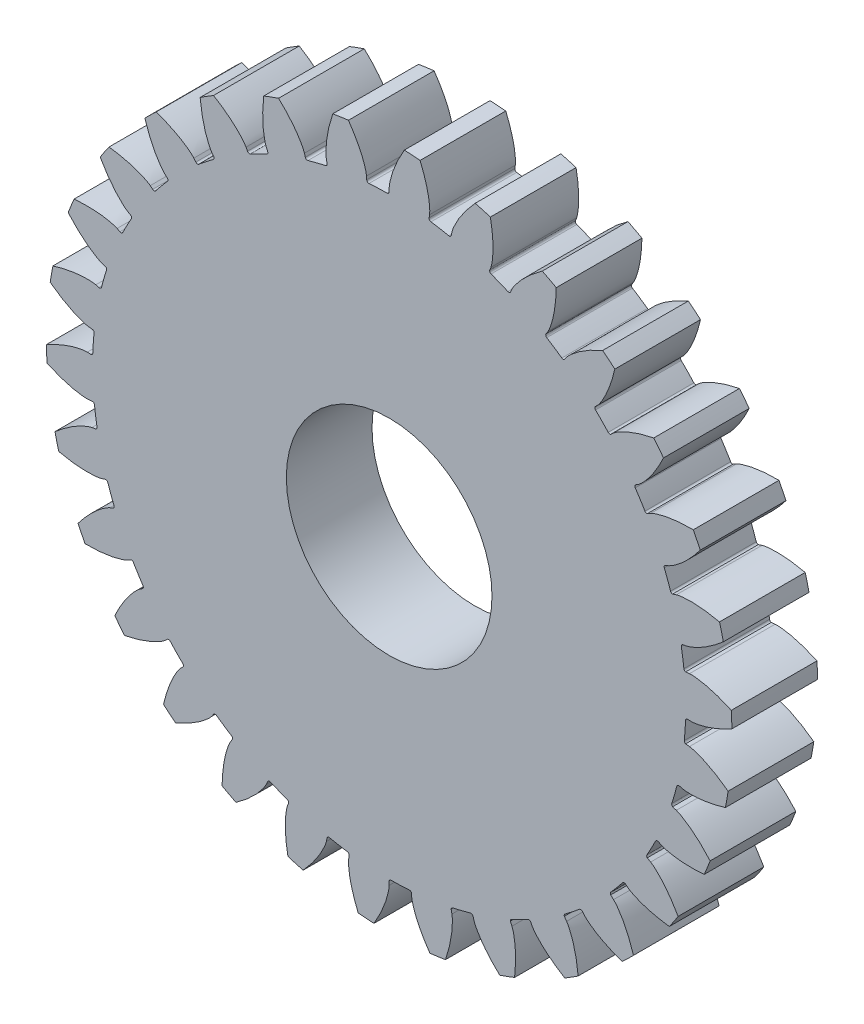
SolidWorks part; units mm, degrees
ref_plane "Alzado" through (0, 0, 0) normal (0, 0, 1) x (1, 0, 0)
ref_plane "Planta" through (0, 0, 0) normal (0, 1, 0) x (1, 0, 0)
ref_plane "Vista lateral" through (0, 0, 0) normal (1, 0, 0) x (0, 0, -1)
sketch "Croquis1" plane through (0, 0, 0) normal (0, 0, 1) x (1, 0, 0)
  line L0 (0, 0) -> (131.0885, 0) construction
  line L1 (0, 0) -> (0, 30) construction
  line L2 (0, 0) -> (12.4587, 12.4587) construction
  line L3 (12.4587, 12.4587) -> (2.6737, 22.2437) construction
  line L4 (0, 0) -> (11.3254, 13.4971) construction
  line L5 (11.3254, 13.4971) -> (1.9027, 21.4038) construction
  line L6 (0, 0) -> (10.106, 14.4328) construction
  line L7 (10.106, 14.4328) -> (1.2895, 20.6062) construction
  line L8 (0, 0) -> (8.8096, 15.2587) construction
  line L9 (8.8096, 15.2587) -> (0.8202, 19.8714) construction
  line L10 (0, 0) -> (7.4462, 15.9685) construction
  line L11 (7.4462, 15.9685) -> (0.4787, 19.2175) construction
  line L12 (0, 0) -> (6.0261, 16.5567) construction
  line L13 (6.0261, 16.5567) -> (0.2468, 18.6602) construction
  line L14 (0, 0) -> (4.5602, 17.0189) construction
  line L15 (4.5602, 17.0189) -> (0.1047, 18.2127) construction
  line L16 (0, 0) -> (3.0595, 17.3516) construction
  line L17 (3.0595, 17.3516) -> (0.0311, 17.8856) construction
  line L18 (0, 0) -> (1.5356, 17.5522) construction
  line L19 (1.5356, 17.5522) -> (0.0039, 17.6862) construction
  circle A0 centre (0, 0) radius 17.6192 construction
  circle A1 centre (0, 0) radius 17.3038 construction
  circle A2 centre (0, 0) radius 20 construction
  circle A3 centre (0, 0) radius 18.75 construction
  spline S0 degree 3 poles (0, 17.6192) (0.003, 17.7087) (0.0309, 17.9084) (0.1107, 18.2574) (0.255, 18.7048) (0.4889, 19.2621) (0.8326, 19.916) (1.5096, 20.9709) (2.1682, 21.7377) (2.6737, 22.2437) knots 0 0 0 0 0.049384 0.111113 0.197533 0.308643 0.444446 0.604939 1 1 1 1
  point P3 (87.284, 1.25)
  point P4 (102.0506, 30)
  point P5 (119.8936, 20)
  point P29 (0, 17.6192)
  dimension "Diámetro de paso (D)" = 37.5
  dimension "Diámetro de raiz" = 34.6075
  dimension "D1" = 40
  dimension "D2" = 35.2385
  dimension "Módulo (m)" = 1.25
  dimension "Número de dientes (N)" = 30
  dimension "Ángulo de presión (AP)" = 20
  dimension "D3" = 45
  dimension "D4" = 13.8381
  dimension "D5" = 40
  dimension "D6" = 12.3005
  dimension "D7" = 35
  dimension "D8" = 10.763
  dimension "D9" = 9.2254
  dimension "D10" = 30
  dimension "D11" = 25
  dimension "D12" = 7.6878
  dimension "D13" = 20
  dimension "D14" = 6.1503
  dimension "D15" = 15
  dimension "D16" = 4.6127
  dimension "D17" = 10
  dimension "D18" = 3.0751
  dimension "D19" = 5
  dimension "D20" = 1.5376
sketch "Croquis2" plane through (0, 0, 0) normal (0, 0, 1) x (1, 0, 0)
  line L0 (56.3227, 9.5882) -> (76.5884, 9.5882) construction
  line L1 (0, 17.3911) -> (0, 17.6192)
  line L2 (0, 0) -> (0.3802, 25.5087) construction
  line L3 (0, 0) -> (3.1082, 25.8589) construction
  line L4 (0, 0) -> (32.6464, 0) construction
  line L5 (0, 0) -> (131.0885, 0) construction
  line L6 (0, 0) -> (1.6991, 25.221) construction
  line L7 (2.3325, 17.2754) -> (2.3632, 17.46)
  line L8 (57.5292, -20.4598) -> (78.7754, -20.4598) construction
  circle A0 centre (0, 0) radius 17.3038 construction
  circle A1 centre (0, 0) radius 20 construction
  arc A2 (-0.1185, 17.3033) -> (2.4382, 17.1311) centre (0, 0) ccw
  arc A3 (1.8037, 19.9185) -> (0.8841, 19.9804) centre (0, 0) ccw
  circle A4 centre (0, 0) radius 18.75 construction
  circle A5 centre (0, 0) radius 6
  arc A6 (2.3325, 17.2754) -> (2.4382, 17.1311) centre (2.4558, 17.2549) ccw
  arc A7 (0, 17.3911) -> (-0.1185, 17.3033) centre (-0.1193, 17.4283) cw
  spline S0 degree 3 poles (1999.6387, -5.2987) (13.6797, 2.6109) (-1.3181, 12.0138) (0.1107, 18.2574) (0.255, 18.7048) (0.4889, 19.2621) (0.8326, 19.916) (20.139, 49.9979) (181.5845, -20.662) (-1997.0603, 11.1311) knots -3.336491 -3.336491 -3.336491 -3.336491 0.049384 0.111113 0.197533 0.308643 0.444446 0.604939 20.022687 20.022687 20.022687 20.022687 only from (0, 17.6192) to (2.6737, 22.2437) construction
  spline S1 degree 3 poles (0, 17.6192) (0.003, 17.7087) (0.0309, 17.9084) (0.1107, 18.2574) (0.255, 18.7048) (0.4889, 19.2621) (0.7168, 19.6957) (0.8626, 19.9442) (0.8841, 19.9804) knots 0 0 0 0 0.049384 0.111113 0.197533 0.308643 0.444446 0.467706 0.467706 0.467706 0.467706
  spline S2 degree 3 poles (2.3632, 17.46) (2.3722, 17.5491) (2.3714, 17.7508) (2.339, 18.1073) (2.2561, 18.57) (2.0991, 19.1536) (1.9314, 19.6139) (1.8202, 19.8797) (1.8037, 19.9185) knots 0 0 0 0 0.049384 0.111113 0.197533 0.308643 0.444446 0.467706 0.467706 0.467706 0.467706
  point P8 (0.2795, 18.7479)
  point P13 (28.0519, 1.9635)
  point P22 (68.2533, 14.5882)
  point P25 (68.2533, 9.5402)
  dimension "Diámetro del cubo" = 12
  dimension "Redondeo" = 0.125
  dimension "Espesor del diente (T)" = 1.9635
  dimension "D1" = 6
  dimension "D2" = 3
  dimension "Espesor del engrane" = 5
  dimension "dientes" = 30
extrude "Saliente-Extruir1" add sketch "Croquis2" along normal blind 5
pattern_circular "MatrizC6" count 30 over 360 about axis through (0, 0, 5) along (0, 0, -1) of "Saliente-Extruir1"
equation "\"Diámetro de paso (D)@Croquis1\"=\"Módulo (m)@Croquis1\"*\"Número de dientes (N)@Croquis1\""
equation "\"Diámetro de raiz@Croquis1\"=(\"Diámetro de paso (D)@Croquis1\")-((2.314)*(\"Módulo (m)@Croquis1\"))"
equation "\"D1@Croquis1\"=(\"Diámetro de paso (D)@Croquis1\")+((2)*(\"Módulo (m)@Croquis1\"))"
equation "\"D2@Croquis1\"=(\"Diámetro de paso (D)@Croquis1\")*(cos( \"Ángulo de presión (AP)@Croquis1\"))"
equation "\"D4@Croquis1\"=(\"D2@Croquis1\"/(2))*((\"D3@Croquis1\")*(PI)/(180))"
equation "\"D6@Croquis1\"=(\"D2@Croquis1\"/(2))*((\"D5@Croquis1\")*(PI)/(180))"
equation "\"D8@Croquis1\"=(\"D2@Croquis1\"/(2))*((\"D7@Croquis1\")*(PI)/(180))"
equation "\"D9@Croquis1\"=(\"D2@Croquis1\"/(2))*((\"D10@Croquis1\")*(PI)/(180))"
equation "\"D12@Croquis1\"=(\"D2@Croquis1\"/(2))*((\"D11@Croquis1\")*(PI)/(180))"
equation "\"D14@Croquis1\"=(\"D2@Croquis1\"/(2))*((\"D13@Croquis1\")*(PI)/(180))"
equation "\"D16@Croquis1\"=(\"D2@Croquis1\"/(2))*((\"D15@Croquis1\")*(PI)/(180))"
equation "\"D18@Croquis1\"=(\"D2@Croquis1\"/(2))*((\"D17@Croquis1\")*(PI)/(180))"
equation "\"D20@Croquis1\"=(\"D2@Croquis1\"/(2))*((\"D19@Croquis1\")*(PI)/(180))"
equation "\"Espesor del diente (T)@Croquis2\"=(1.5708)*(\"Módulo (m)@Croquis1\")"
equation "\"D1@Croquis2\"=(\"Espesor del diente (T)@Croquis2\"/(\"Diámetro de paso (D)@Croquis1\"/2))*(180/PI)"
equation "\"D2@Croquis2\"=\"D1@Croquis2\"/2"
equation "\"D1@Saliente-Extruir1\"=\"Espesor del engrane@Croquis2\""
equation "\"dientes@Croquis2\"=\"Número de dientes (N)@Croquis1\""
equation "\"Redondeo@Croquis2\"=\"Módulo (m)@Croquis1\"*(0.1)"
equation "\"D1@MatrizC6\"=\"Número de dientes (N)@Croquis1\""
